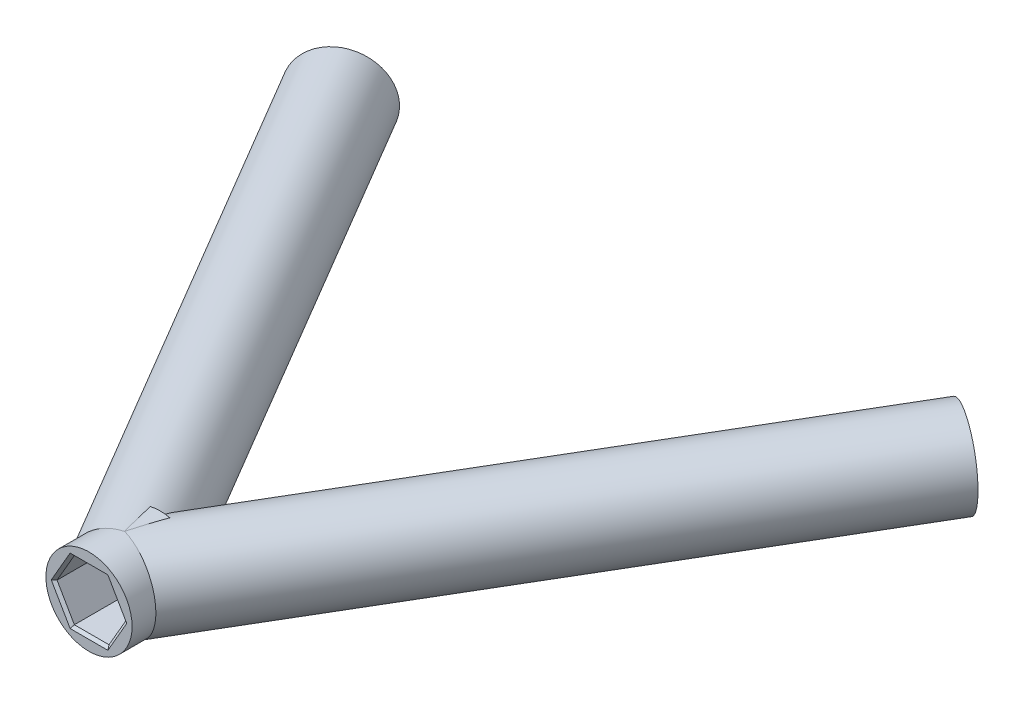
SolidWorks part; units mm, degrees
material "ABS"
ref_plane "Front Plane" through (0, 0, 0) normal (0, 0, 1) x (1, 0, 0)
ref_plane "Top Plane" through (0, 0, 0) normal (0, 1, 0) x (1, 0, 0)
ref_plane "Right Plane" through (0, 0, 0) normal (1, 0, 0) x (0, 0, -1)
sketch "Sketch1" plane through (0, 0, 0) normal (0, 1, 0) x (1, 0, 0)
  line L0 (0, 0) -> (-35.5851, 85.91) construction
  line L1 (0, 0) -> (35.5851, 85.91) construction
  line L2 (0, 0) -> (0, 85.91) construction
  line L3 (0, 17.5) -> (0, 24.1)
  line L4 (-28.8881, 69.7421) -> (0, 20.8) construction
  line L5 (0, 20.8) -> (28.8881, 69.7421) construction
  point P3 (0, 17.5)
  point P6 (-28.8881, 69.7421)
  point P7 (28.8881, 69.7421)
  point P10 (0, 20.8)
  dimension "D1" = 45
  dimension "D2" = 85.91
  dimension "D3" = 17.5
  dimension "D4" = 17.5
  dimension "D5" = 17.5
  dimension "D6" = 6.6
  dimension "D7" = 61.103
revolve "Revolve-Thin1" add sketch "Sketch1" angle 360 about L2 wall 4
sketch "Sketch3" plane through (0, 0, 0) normal (0, 1, 0) x (1, 0, 0)
  line L0 (-28.8881, 69.7421) -> (0, 20.8) construction
  line L1 (-28.8881, 69.7421) -> (0, 20.8)
revolve "Revolve-Thin2" add sketch "Sketch3" angle 360 about L1 wall 4
sketch "Sketch4" plane through (0, 0, 0) normal (0, 1, 0) x (1, 0, 0)
  line L0 (0, 20.8) -> (28.8881, 69.7421) construction
  line L1 (0, 20.8) -> (28.8881, 69.7421)
revolve "Revolve-Thin3" add sketch "Sketch4" angle 360 about L1 wall 4
sketch "Sketch5" plane through (-37.9932, 0, -64.3678) normal (-0.5083, 0, -0.8612) x (-0.8612, 0, 0.5083)
  line L1 (-8.9649, 2.785) -> (-12.1808, 2.785)
  line L2 (-12.1808, 2.785) -> (-13.7887, 0)
  line L3 (-13.7887, 0) -> (-12.1808, -2.785)
  line L4 (-12.1808, -2.785) -> (-8.9649, -2.785)
  line L5 (-8.9649, -2.785) -> (-7.357, 0)
  line L6 (-7.357, 0) -> (-8.9649, 2.785)
  circle A0 centre (-10.5728, 0) radius 2.785 construction
  circle A1 centre (-10.5728, 0) radius 4
  circle A2 centre (-10.5728, 0) radius 4 construction
  dimension "D2" = 5.57
  dimension "D1" = 0
extrude "Cut-Extrude1" cut sketch "Sketch5" against normal blind 6.6
sketch "Sketch6" plane through (0, 0, -17.5) normal (0, 0, 1) x (1, 0, 0)
  line L1 (1.6079, 2.785) -> (-1.6079, 2.785)
  line L2 (-1.6079, 2.785) -> (-3.2158, 0)
  line L3 (-3.2158, 0) -> (-1.6079, -2.785)
  line L4 (-1.6079, -2.785) -> (1.6079, -2.785)
  line L5 (1.6079, -2.785) -> (3.2158, 0)
  line L6 (3.2158, 0) -> (1.6079, 2.785)
  circle A0 centre (0, 0) radius 2.785 construction
  dimension "D1" = 5.57
extrude "Cut-Extrude2" cut sketch "Sketch6" against normal blind 6.6
sketch "Sketch7" plane through (37.9932, 0, -64.3678) normal (0.5083, 0, -0.8612) x (-0.8612, 0, -0.5083)
  line L1 (12.1808, 2.785) -> (8.9649, 2.785)
  line L2 (8.9649, 2.785) -> (7.357, 0)
  line L3 (7.357, 0) -> (8.9649, -2.785)
  line L4 (8.9649, -2.785) -> (12.1808, -2.785)
  line L5 (12.1808, -2.785) -> (13.7887, 0)
  line L6 (13.7887, 0) -> (12.1808, 2.785)
  circle A0 centre (10.5728, 0) radius 2.785 construction
  dimension "D1" = 5.57
extrude "Cut-Extrude3" cut sketch "Sketch7" against normal blind 6.6
chamfer "Chamfer1" distance 0.25 angle 45 18 edges at (-28.8881, 2.785, -69.7421) (-30.9652, 1.3925, -68.5161) (-30.9652, -1.3925, -68.5161) (-28.8881, -2.785, -69.7421) (-26.8111, 1.3925, -70.9681) (-26.8111, -1.3925, -70.9681) (2.4119, -1.3925, -17.5) (2.4119, 1.3925, -17.5) (0, 2.785, -17.5) (-2.4119, 1.3925, -17.5) (-2.4119, -1.3925, -17.5) (0, -2.785, -17.5) (28.8881, 2.785, -69.7421) (26.8111, 1.3925, -70.9681) (26.8111, -1.3925, -70.9681) (28.8881, -2.785, -69.7421) (30.9652, 1.3925, -68.5161) (30.9652, -1.3925, -68.5161)
